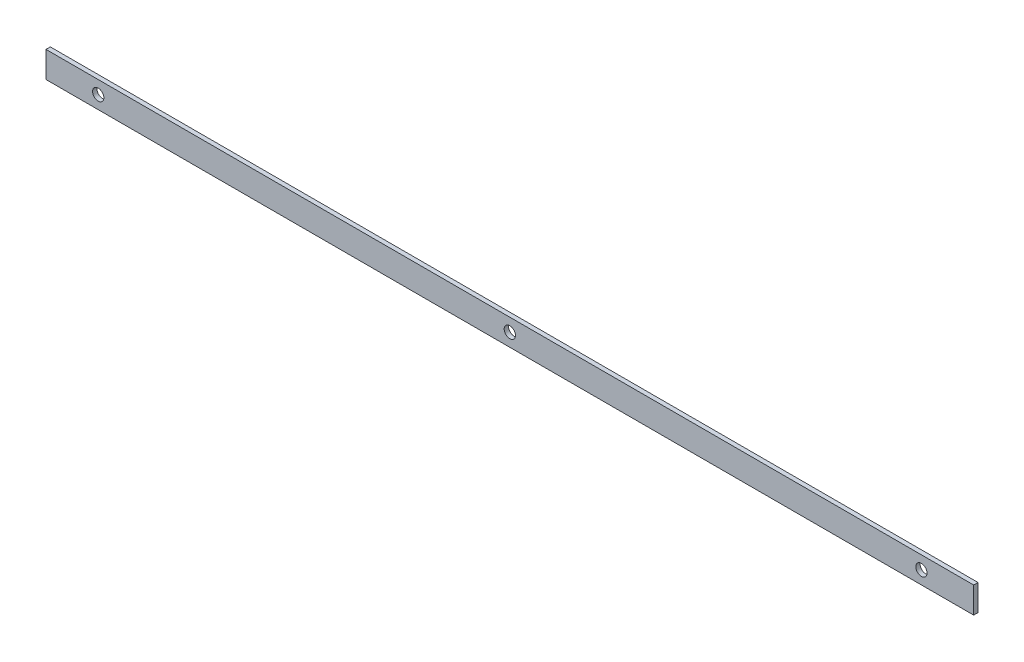
SolidWorks part; units mm, degrees
ref_plane "Plan de face" through (0, 0, 0) normal (0, 0, 1) x (1, 0, 0)
ref_plane "Plan de dessus" through (0, 0, 0) normal (0, 1, 0) x (1, 0, 0)
ref_plane "Plan de droite" through (0, 0, 0) normal (1, 0, 0) x (0, 0, -1)
sketch "Esquisse1" plane through (0, 0, 0) normal (0, 0, 1) x (1, 0, 0)
  line L0 (-533, 0) -> (533, 0)
other "Elément mécano-soudé1"
ref_plane "Plan1" through (-533, 0, 0) normal (1, 0, 0) x (0, 1, 0)
sketch "plat" plane through (-533, 0, 0) normal (1, 0, 0) x (0, 1, 0)
  line L0 (-15, 0) -> (15, 0) construction
  line L1 (-15, 2.5) -> (15, 2.5)
  line L2 (-15, 2.5) -> (-15, -2.5)
  line L3 (-15, -2.5) -> (15, -2.5)
  line L4 (15, 2.5) -> (15, -2.5)
  line L5 (0, 2.5) -> (0, -2.5) construction
  point P8 (0, 0)
  dimension "B" = 30
  dimension "A" = 5
sketch "Esquisse2" plane through (0, 0, -2.5) normal (0, 0, -1) x (-1, 0, 0)
  line L0 (533, 0) -> (-533, 0) construction
  line L1 (533, -15) -> (533, 15) construction
  line L2 (-533, -15) -> (-533, 15) construction
  point P0 (473, 0)
  point P5 (-473, 0)
ref_plane "Plan2" through (473, 0, 0) normal (1, 0, 0) x (0, 0, -1)
hole_wizard "Diamètre du perçage Ø13.0 (13)1" positions "Esquisse3" profile "Esquisse4" hole size "Ø13.0" standard "ISO" end condition through all
sketch "Esquisse3" plane through (0, 0, -2.5) normal (0, 0, -1) x (-1, 0, 0)
  point P0 (473, 0)
sketch "Esquisse4" plane through (-473, 0, -2.5) normal (1, 0, 0) x (0, 1, 0)
  line L0 (0, 0) -> (0, 5)
  line L1 (0, 5) -> (6.5, 5)
  line L2 (6.5, 5) -> (6.5, 0)
  line L5 (6.5, 0) -> (0, 0)
  line L11 (0, -6.35) -> (0, 107.95) construction
  dimension "Diamètre du perçage jusqu'au prochain" = 13
  dimension "Profondeur du perçage jusqu'au prochain" = 5
pattern_linear "Répétition linéaire2" count 3 spacing 473 along (1, 0, 0) of "Diamètre du perçage Ø13.0 (13)1"
equation "\"D2@Esquisse2\"=\"D1@Esquisse2\""
